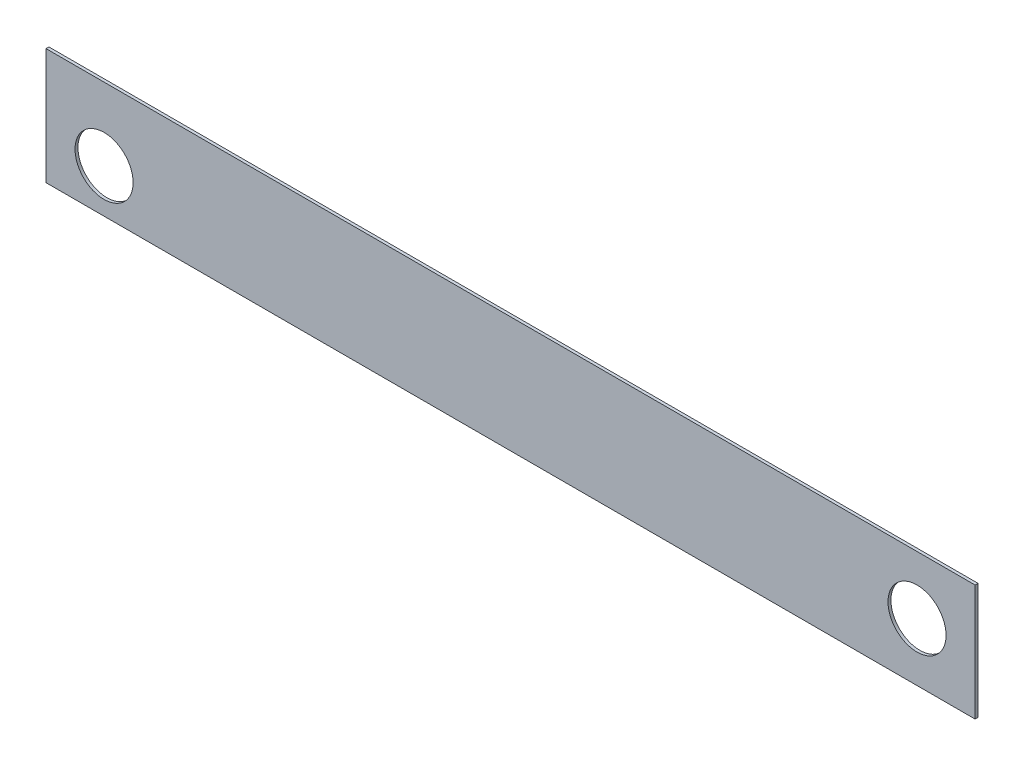
SolidWorks part; units mm, degrees
ref_plane "Plane1" through (0, 0, 0) normal (0, 0, 1) x (1, 0, 0)
ref_plane "Plane2" through (0, 0, 0) normal (0, 1, 0) x (1, 0, 0)
ref_plane "Plane3" through (0, 0, 0) normal (1, 0, 0) x (0, 0, -1)
sketch "Sketch1" plane through (0, 0, 0) normal (0, 0, 1) x (1, 0, 0)
  line L1 (-20, 25) -> (300, 25)
  line L2 (-20, 25) -> (-20, -15)
  line L3 (-20, -15) -> (300, -15)
  line L4 (300, 25) -> (300, -15)
  circle A0 centre (0, 0) radius 10
  circle A1 centre (280, 5) radius 10
  dimension "D7" = 20
  dimension "D1" = 20
  dimension "D2" = 20
  dimension "D3" = 15
  dimension "D4" = 280
  dimension "D5" = 40
  dimension "D6" = 20
extrude "Extrude1" add sketch "Sketch1" along normal blind 1
